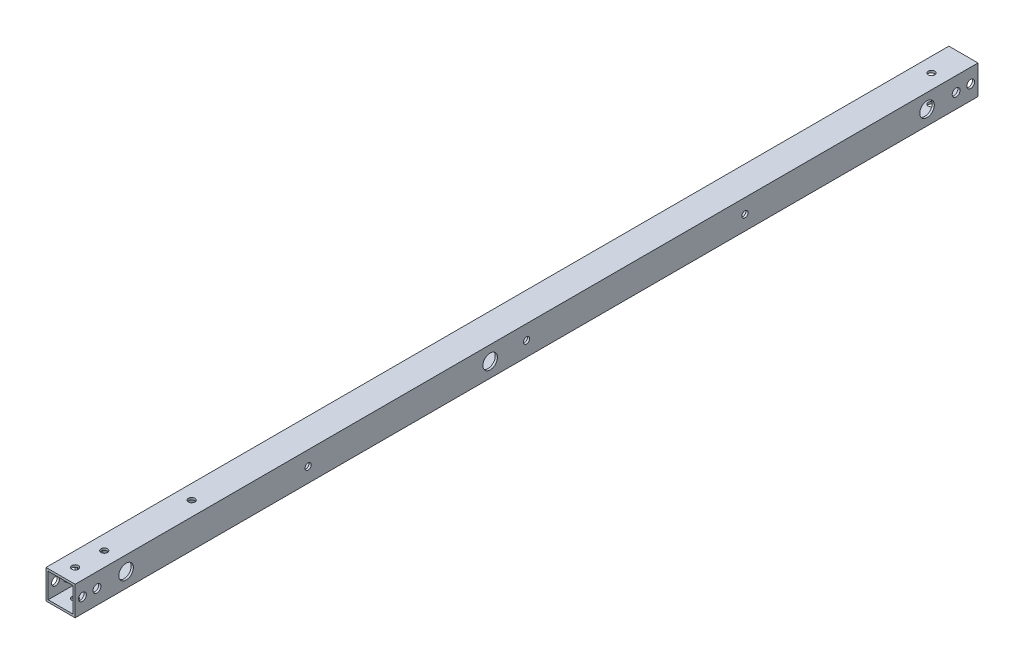
SolidWorks part; units mm, degrees
material "6063-T5"
ref_plane "正面" through (0, 0, 0) normal (0, 0, 1) x (1, 0, 0)
ref_plane "平面" through (0, 0, 0) normal (0, 1, 0) x (1, 0, 0)
ref_plane "右側面" through (0, 0, 0) normal (1, 0, 0) x (0, 0, -1)
sketch "ｽｹｯﾁ1" plane through (0, 0, 0) normal (0, 0, 1) x (1, 0, 0)
  line L1 (-10, -10) -> (10, -10)
  line L2 (-10, -10) -> (-10, 10)
  line L3 (-10, 10) -> (10, 10)
  line L4 (10, -10) -> (10, 10)
  line L5 (-10, -10) -> (10, 10) construction
  line L6 (-10, 10) -> (10, -10) construction
  line L7 (-8.5, -8.5) -> (8.5, -8.5)
  line L8 (-8.5, -8.5) -> (-8.5, 8.5)
  line L9 (-8.5, 8.5) -> (8.5, 8.5)
  line L10 (8.5, -8.5) -> (8.5, 8.5)
  line L11 (-8.5, -8.5) -> (8.5, 8.5) construction
  line L12 (-8.5, 8.5) -> (8.5, -8.5) construction
  point P0 (0, 0)
  point P6 (0, 0)
  dimension "D1" = 1.5
  dimension "D2" = 20
  dimension "D3" = 20
extrude "ﾎﾞｽ - 押し出し1" add sketch "ｽｹｯﾁ1" along normal blind 620
sketch "ｽｹｯﾁ2" plane through (10, 0, 0) normal (1, 0, 0) x (0, 0, -1)
  line L0 (-620, -10) -> (0, -10) construction
  line L1 (-620, -10) -> (-620, 10) construction
  circle A4 centre (-585, 0) radius 2.7
  circle A9 centre (-35, 0) radius 2.7
  circle A14 centre (-335, 0) radius 2.7
  dimension "D1" = 5.4
  dimension "D2" = 550
  dimension "D3" = 10
  dimension "D6" = 2
  dimension "D7" = 250
  dimension "D4" = 2
  dimension "D5" = 35
extrude "ｶｯﾄ - 押し出し1" cut sketch "ｽｹｯﾁ2" against normal blind 25
sketch "ｽｹｯﾁ3" plane through (0, 10, 0) normal (0, 1, 0) x (1, 0, 0)
  line L2 (10, -620) -> (10, 0) construction
  line L3 (10, 0) -> (-10, 0) construction
  circle A1 centre (0, -22) radius 2.25
  circle A6 centre (0, -610) radius 2.25
  circle A7 centre (0, -530) radius 2.25
  circle A8 centre (0, -590) radius 2.25
  dimension "D2" = 22
  dimension "D3" = 4.5
  dimension "D7" = 80
  dimension "D8" = 2
  dimension "D9" = 10
  dimension "D11" = 10
  dimension "D4" = 10
  dimension "D5" = 4.5
  dimension "D10" = 20
  dimension "D6" = 2
extrude "ｶｯﾄ - 押し出し2" cut sketch "ｽｹｯﾁ3" against normal blind 25
sketch "ｽｹｯﾁ4" plane through (10, 0, 0) normal (1, 0, 0) x (0, 0, -1)
  line L0 (0, 8.5) -> (0, -8.5) construction
  line L1 (-620, 10) -> (0, 10) construction
  line L2 (0, -10) -> (0, 10) construction
  line L3 (-620, -10) -> (0, -10) construction
  line L4 (-620, -10) -> (-620, 10) construction
  circle A0 centre (-15, 0) radius 2.7
  circle A1 centre (-5, 0) radius 2.7
  circle A2 centre (-615, 0) radius 2.7
  circle A3 centre (-605, 0) radius 2.7
  dimension "D1" = 15
  dimension "D2" = 10
  dimension "D3" = 5.4
  dimension "D4" = 5.4
  dimension "D5" = 5.4
  dimension "D6" = 5
  dimension "D7" = 10
  dimension "D8" = 10
  dimension "D9" = 5
  dimension "D11" = 15
  dimension "D10" = 5.4
  dimension "D12" = 10
extrude "ｶｯﾄ - 押し出し3" cut sketch "ｽｹｯﾁ4" against normal blind 40
sketch "ｽｹｯﾁ6" plane through (0, -10, 0) normal (0, -1, 0) x (-1, 0, 0)
  circle A0 centre (0, -530) radius 5
  dimension "D1" = 10
extrude "ｶｯﾄ - 押し出し4" cut sketch "ｽｹｯﾁ6" against normal blind 10
sketch "ｽｹｯﾁ7" plane through (-10, 0, 0) normal (1, 0, 0) x (0, 0, -1)
  circle A0 centre (-585, 0) radius 5
  circle A1 centre (-335, 0) radius 5
  circle A2 centre (-35, 0) radius 5
  dimension "D1" = 10
  dimension "D2" = 10
  dimension "D3" = 10
extrude "ｶｯﾄ - 押し出し5" cut sketch "ｽｹｯﾁ7" along normal blind 20 from offset 10
sketch "ｽｹｯﾁ8" plane through (10, 0, 0) normal (1, 0, 0) x (0, 0, -1)
  circle A0 centre (-605, 0) radius 5
  dimension "D1" = 10
extrude "ｶｯﾄ - 押し出し6" cut sketch "ｽｹｯﾁ8" against normal blind 30 from offset 10 offset against normal yes
sketch "ｽｹｯﾁ9" plane through (-10, 0, 0) normal (-1, 0, 0) x (0, 0, 1)
  circle A0 centre (15, 0) radius 5
  dimension "D1" = 10
extrude "ｶｯﾄ - 押し出し7" cut sketch "ｽｹｯﾁ9" against normal blind 5
sketch "ｽｹｯﾁ10" plane through (10, 0, 0) normal (1, 0, 0) x (0, 0, -1)
  line L0 (-620, -10) -> (-620, 10) construction
  point P0 (-460, 0)
  point P1 (-310, 0)
  point P2 (-160, 0)
  point P5 (-620, 0)
  dimension "D1" = 160
  dimension "D2" = 150
  dimension "D3" = 150
hole_wizard "Ø4.3 (4.3) 直径の穴1" positions "ｽｹｯﾁ10" profile "ｽｹｯﾁ11" hole size "Ø4.3" standard "JIS" end condition through all
sketch "ｽｹｯﾁ11" plane through (10, 0, 460) normal (0, 1, 0) x (0, 0, -1)
  line L0 (0, 0) -> (0, 20)
  line L1 (0, 20) -> (2.15, 20)
  line L2 (2.15, 20) -> (2.15, 0)
  line L5 (2.15, 0) -> (0, 0)
  line L11 (0, -6.35) -> (0, 107.95) construction
  dimension "通し穴の直径" = 4.3
  dimension "通し穴の深さ" = 20
hole_wizard "Ø10.0 (10) 直径の穴1" positions "ｽｹｯﾁ12" profile "ｽｹｯﾁ13" hole size "Ø10.0" standard "JIS"
sketch "ｽｹｯﾁ12" plane through (-10, 0, 0) normal (-1, 0, 0) x (0, 0, 1)
  point P0 (160, 0)
  point P3 (310, 0)
  point P6 (460, 0)
sketch "ｽｹｯﾁ13" plane through (-10, 0, 160) normal (0, 1, 0) x (0, 0, 1)
  line L0 (0, 0) -> (0, 1.5)
  line L1 (0, 1.5) -> (5, 1.5)
  line L2 (5, 1.5) -> (5, 0)
  line L5 (5, 0) -> (0, 0)
  line L10 (0, 1.5) -> (-5, 1.5) construction
  line L11 (0, -6.35) -> (0, 107.95) construction
  dimension "穴の直径" = 10
  dimension "穴の深さ" = 1.5
  dimension "ﾄﾞﾘﾙ角度" = 180
